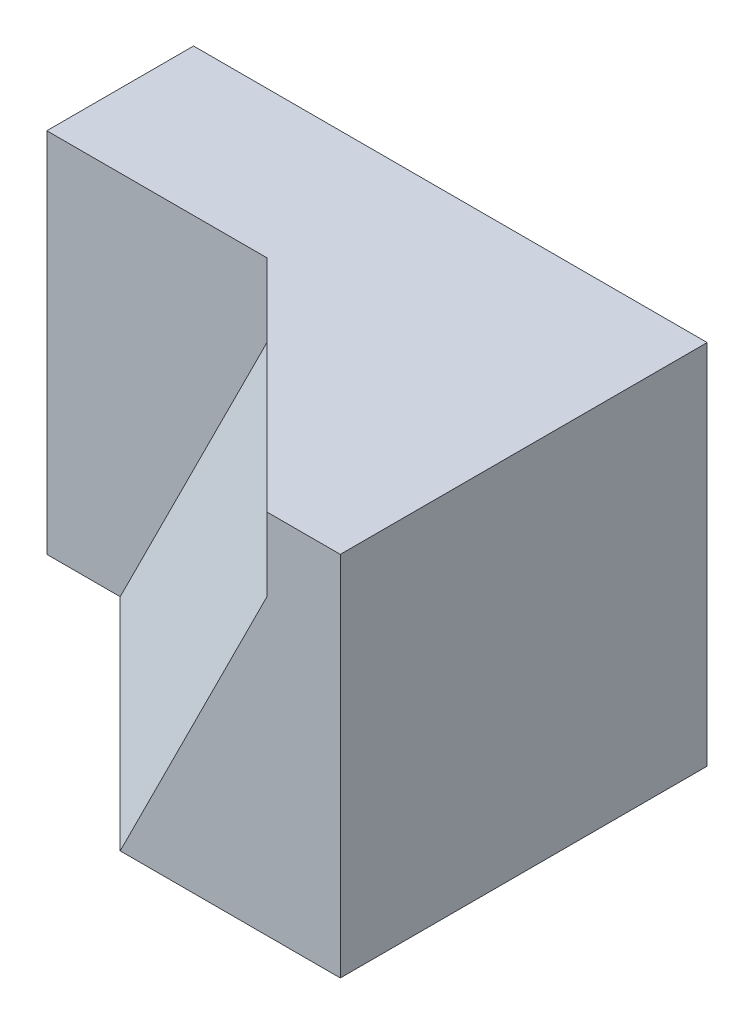
SolidWorks part; units mm, degrees
ref_plane "Front Plane" through (0, 0, 0) normal (0, 0, 1) x (1, 0, 0)
ref_plane "Top Plane" through (0, 0, 0) normal (0, 1, 0) x (1, 0, 0)
ref_plane "Right Plane" through (0, 0, 0) normal (1, 0, 0) x (0, 0, -1)
sketch "Sketch1" plane through (0, 0, 0) normal (0, 0, 1) x (1, 0, 0)
  line L1 (0, 0) -> (70, 0)
  line L2 (0, 0) -> (0, 50)
  line L3 (0, 50) -> (70, 50)
  line L4 (70, 0) -> (70, 50)
  dimension "D1" = 70
  dimension "D2" = 50
extrude "Boss-Extrude1" add sketch "Sketch1" along normal blind 50
sketch "Sketch2" plane through (0, 50, 0) normal (0, 1, 0) x (1, 0, 0)
  line L0 (0, -20) -> (10, -20)
  line L1 (0, -50) -> (0, 0) construction
  line L2 (10, -20) -> (40, -50)
  line L3 (70, -50) -> (0, -50) construction
  line L4 (40, -50) -> (0, -50)
  line L5 (0, -50) -> (0, -20)
  dimension "D1" = 30
  dimension "D2" = 10
  dimension "D3" = 30
extrude "Cut-Extrude1" cut sketch "Sketch2" against normal blind 50
sketch "Sketch3" plane through (0, 50, 0) normal (0, 1, 0) x (1, 0, 0)
  line L0 (10, -20) -> (30, -20)
  line L1 (30, -20) -> (60, -50)
  line L2 (70, -50) -> (40, -50) construction
  line L3 (60, -50) -> (40, -50)
  line L4 (40, -50) -> (10, -20)
  dimension "D1" = 20
extrude "Cut-Extrude2" cut sketch "Sketch3" against normal blind 40
ref_plane "Plane1" through (-4.6296, 1.8519, 4.6296) normal (0.6804, -0.2722, -0.6804) x (-0.7328, -0.2527, -0.6317)
sketch "Sketch7" plane through (0, 0, 50) normal (0, 0, 1) x (1, 0, 0)
  line L0 (60, 10) -> (60, 50) construction
  line L1 (60, 50) -> (30, 50) construction
  point P0 (60, 40)
  dimension "D1" = 10
sketch "Sketch8" plane through (0, 0, 20) normal (0, 0, 1) x (1, 0, 0)
  line L0 (30, 10) -> (30, 50) construction
  point P0 (30, 40)
  dimension "D1" = 10
ref_plane "Plane2" through (-4.4444, 2.2222, 4.4444) normal (0.6667, -0.3333, -0.6667) x (-0.7454, -0.2981, -0.5963)
sketch "Sketch9" plane through (-4.4444, 2.2222, 4.4444) normal (0.6667, -0.3333, -0.6667) x (-0.7454, -0.2981, -0.5963)
  line L0 (-86.4613, 13.4164) -> (-59.6285, -22.3607)
  line L1 (-59.6285, -22.3607) -> (-19.3793, -8.9443)
  line L2 (-19.3793, -8.9443) -> (-86.4613, 13.4164)
extrude "Cut-Extrude4" cut sketch "Sketch9" against normal blind 14
sketch "Sketch10" plane through (-4.4444, 2.2222, 4.4444) normal (0.6667, -0.3333, -0.6667) x (-0.7454, -0.2981, -0.5963)
  line L0 (-59.6285, -22.3607) -> (-19.3793, -8.9443)
  line L1 (-19.3793, -8.9443) -> (-86.4613, 13.4164)
  line L2 (-86.4613, 13.4164) -> (-59.6285, -22.3607)
extrude "Boss-Extrude6" add sketch "Sketch10" along normal blind 14
sketch "Sketch11" plane through (-4.4444, 2.2222, 4.4444) normal (0.6667, -0.3333, -0.6667) x (-0.7454, -0.2981, -0.5963)
  line L0 (-19.3793, -8.9443) -> (-46.2121, 26.8328)
  line L1 (-46.2121, 26.8328) -> (-86.4613, 13.4164)
  line L2 (-86.4613, 13.4164) -> (-19.3793, -8.9443)
extrude "Boss-Extrude7" add sketch "Sketch11" along normal blind 14
sketch "Sketch12" plane through (0, 0, 20) normal (0, 0, 1) x (1, 0, 0)
  line L0 (0, 0) -> (10, 0)
  line L1 (10, 0) -> (10, 10)
  line L2 (10, 10) -> (30, 40)
  line L3 (30, 40) -> (10, 0)
extrude "Cut-Extrude5" cut sketch "Sketch12" along normal blind 14 contours L1 L2 L3
sketch "Sketch13" plane through (-4.4444, 2.2222, 4.4444) normal (-0.6667, 0.3333, 0.6667) x (0.5963, -0.2981, 0.7454)
  line L0 (20.87, 49.1935) -> (20.87, 4.4721)
  line L1 (20.87, 4.4721) -> (61.1192, 17.8885)
  line L2 (61.1192, 17.8885) -> (61.1192, 62.6099)
  line L3 (61.1192, 62.6099) -> (20.87, 49.1935)
extrude "Cut-Extrude6" cut sketch "Sketch13" along normal blind 14
sketch "Sketch14" plane through (0, 0, 0) normal (0, -1, 0) x (1, 0, 0)
  line L1 (0, 0) -> (70, 0)
  line L2 (0, 0) -> (0, 50)
  line L3 (0, 50) -> (70, 50)
  line L4 (70, 0) -> (70, 50)
extrude "Cut-Extrude7" cut sketch "Sketch14" along normal blind 14
sketch "Sketch15" plane through (0, 0, 50) normal (0, 0, 1) x (1, 0, 0)
  line L0 (45, 10) -> (60, 40)
  line L1 (60, 40) -> (60, 10)
  line L2 (60, 10) -> (45, 10)
extrude "Boss-Extrude8" add sketch "Sketch15" against normal blind 14
